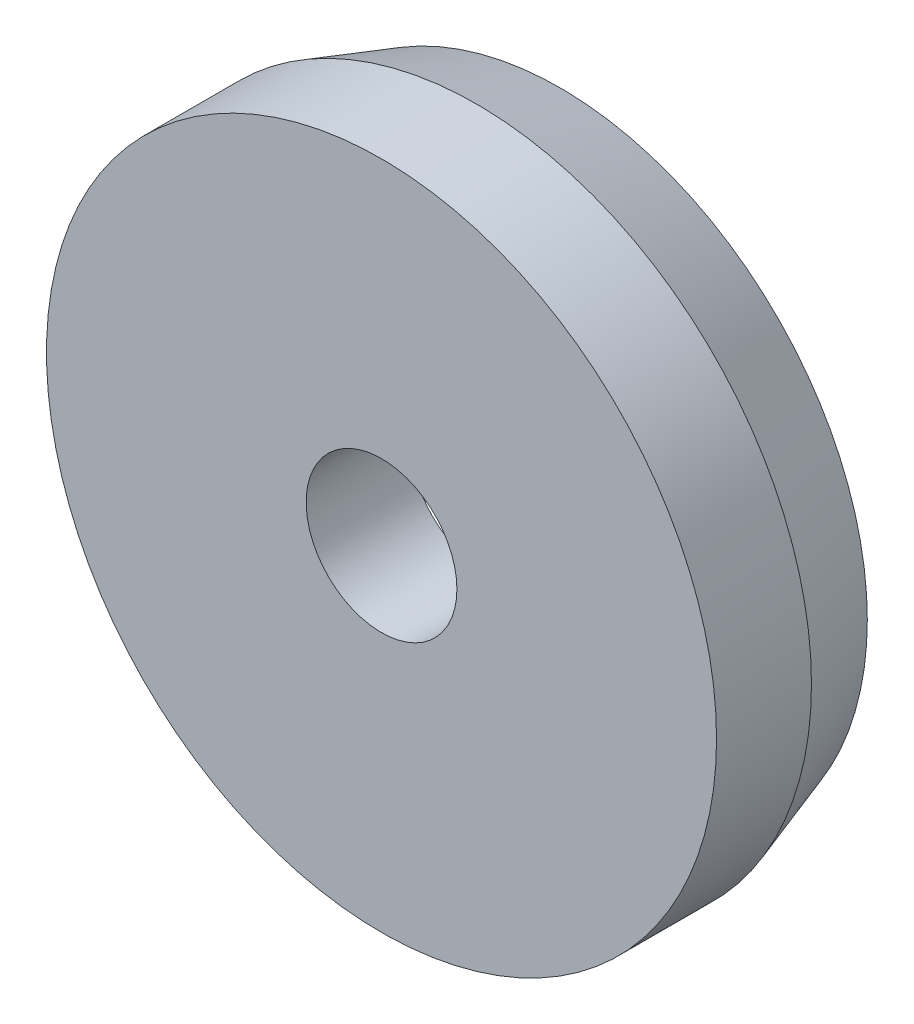
SolidWorks part; units mm, degrees
ref_plane "Alzado" through (0, 0, 0) normal (0, 0, 1) x (1, 0, 0)
ref_plane "Planta" through (0, 0, 0) normal (0, 1, 0) x (1, 0, 0)
ref_plane "Vista lateral" through (0, 0, 0) normal (1, 0, 0) x (0, 0, -1)
ref_plane "Plane1" through (0, -10.25, 0) normal (0, 1, 0) x (1, 0, 0)
sketch "Sketch1" plane through (0, -10.25, 0) normal (0, 1, 0) x (1, 0, 0)
  line L0 (0.6, 1.84) -> (0.55, 1.99)
  line L1 (0.55, 1.99) -> (0.38, 1.99)
  line L2 (0.135, 1.8566) -> (0.135, 1.67)
  line L3 (0.135, 1.67) -> (0.6, 1.67)
  line L4 (0.6, 1.67) -> (0.6, 1.84)
  line L5 (0, 1.99) -> (0, 1.67) construction
  arc A0 (0.38, 1.99) -> (0.135, 1.8566) centre (0, 2.3963) cw
  dimension "D1" = 0.5563
  dimension "D2" = 0.135
  dimension "D3" = 0.38
  dimension "D4" = 0.55
  dimension "D5" = 0.6
  dimension "D6" = 0.17
  dimension "D7" = 0.1866
revolve "Revolve1" add sketch "Sketch1" angle 360 about L5
